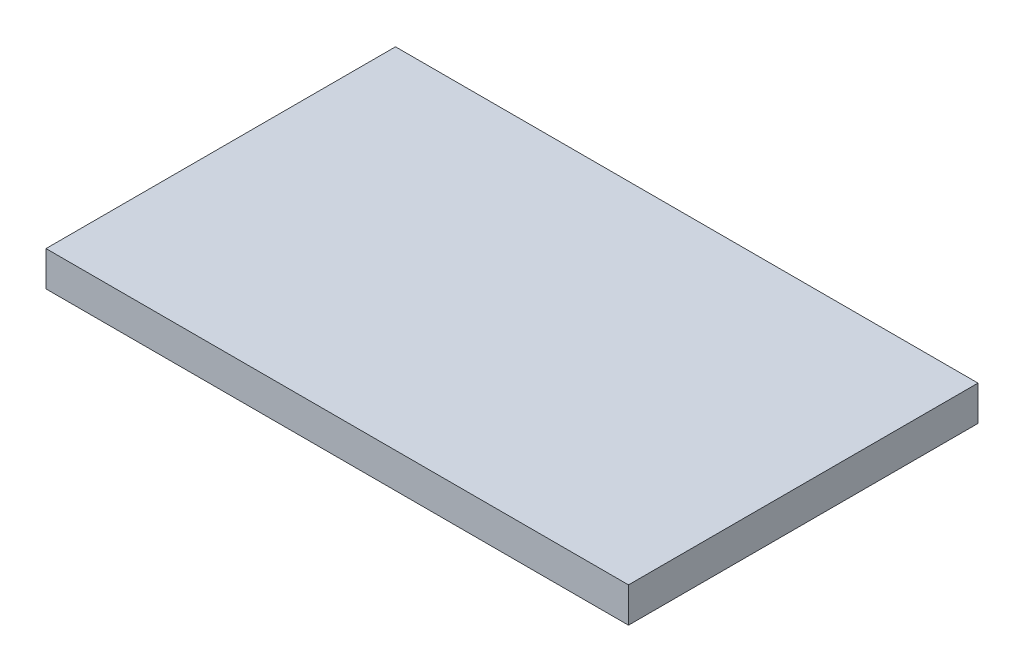
SolidWorks part; units mm, degrees
material "Epoxy Resin"
ref_plane "Front Plane" through (0, 0, 0) normal (0, 0, 1) x (1, 0, 0)
ref_plane "Top Plane" through (0, 0, 0) normal (0, 1, 0) x (1, 0, 0)
ref_plane "Right Plane" through (0, 0, 0) normal (1, 0, 0) x (0, 0, -1)
sketch "Sketch1" plane through (0, 0, 0) normal (0, 1, 0) x (1, 0, 0)
  line L1 (0, 0) -> (25, 0)
  line L2 (0, 0) -> (0, 15)
  line L3 (0, 15) -> (25, 15)
  line L4 (25, 0) -> (25, 15)
  dimension "D1" = 15
  dimension "D2" = 25
extrude "Boss-Extrude1" add sketch "Sketch1" along normal blind 1.5
